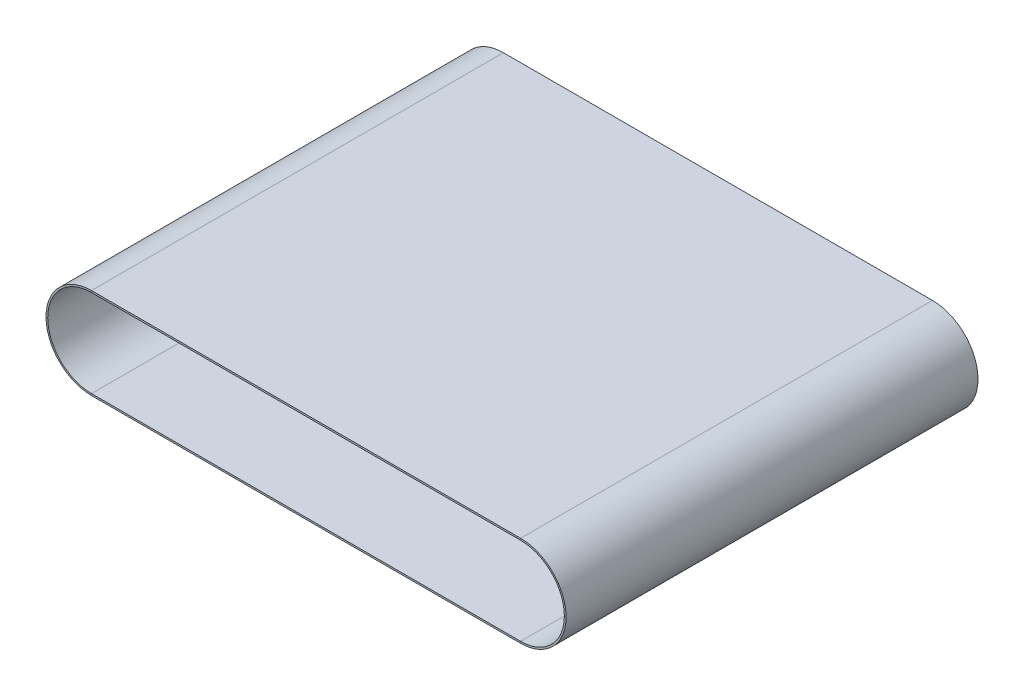
SolidWorks part; units mm, degrees
ref_plane "Front Plane" through (0, 0, 0) normal (0, 0, 1) x (1, 0, 0)
ref_plane "Top Plane" through (0, 0, 0) normal (0, 1, 0) x (1, 0, 0)
ref_plane "Right Plane" through (0, 0, 0) normal (1, 0, 0) x (0, 0, -1)
sketch "Sketch1" plane through (0, 0, 0) normal (0, 0, 1) x (1, 0, 0)
  line L0 (-250, -25.5) -> (0, -25.5)
  line L1 (0, 25.5) -> (-250, 25.5)
  arc A1 (-250, 25.5) -> (-250, -25.5) centre (-250, 0) ccw
  arc A3 (0, -25.5) -> (0, 25.5) centre (0, 0) ccw
  dimension "D1" = 51
  dimension "D2" = 250
sketch "Sketch2" plane through (0, 0, 0) normal (1, 0, 0) x (0, 0, -1)
  line L1 (-120, 25.5) -> (120, 25.5)
  line L2 (-120, 25.5) -> (-120, 26.5)
  line L3 (-120, 26.5) -> (120, 26.5)
  line L4 (120, 25.5) -> (120, 26.5)
  point P4 (0, 25.5)
  dimension "D1" = 1
  dimension "D2" = 240
sweep "Sweep1" add profiles "Sketch2" path "Sketch1"
